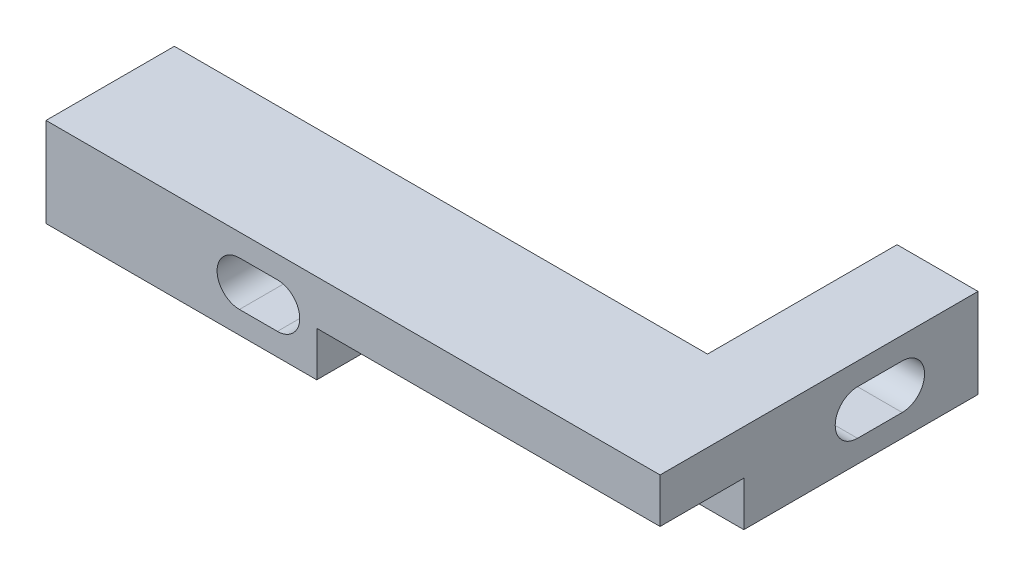
SolidWorks part; units mm, degrees
ref_plane "Front Plane" through (0, 0, 0) normal (0, 0, 1) x (1, 0, 0)
ref_plane "Top Plane" through (0, 0, 0) normal (0, 1, 0) x (1, 0, 0)
ref_plane "Right Plane" through (0, 0, 0) normal (1, 0, 0) x (0, 0, -1)
sketch "Sketch1" plane through (0, 0, 0) normal (0, 1, 0) x (1, 0, 0)
  line L1 (-27.5, 12.5) -> (27.5, 12.5)
  line L2 (-27.5, 12.5) -> (-27.5, -12.5)
  line L3 (-27.5, -12.5) -> (27.5, -12.5)
  line L4 (27.5, 12.5) -> (27.5, -12.5)
  line L5 (-27.5, 12.5) -> (27.5, -12.5) construction
  line L6 (-27.5, -12.5) -> (27.5, 12.5) construction
  point P0 (0, 0)
  dimension "D1" = 55
  dimension "D2" = 25
extrude "Boss-Extrude1" add sketch "Sketch1" along normal blind 4
sketch "Sketch5" plane through (0, 4, 0) normal (0, 1, 0) x (1, 0, 0)
  line L1 (-20.25, 8.5) -> (20.25, 8.5)
  line L2 (-20.25, 8.5) -> (-20.25, -8.5)
  line L3 (-20.25, -8.5) -> (20.25, -8.5)
  line L4 (20.25, 8.5) -> (20.25, -8.5)
  line L5 (-20.25, 8.5) -> (20.25, -8.5) construction
  line L6 (-20.25, -8.5) -> (20.25, 8.5) construction
  point P0 (0, 0)
  dimension "D1" = 17
  dimension "D2" = 40.5
extrude "Cut-Extrude2" cut sketch "Sketch5" against normal through all
sketch "Sketch6" plane through (0, 4, 0) normal (0, 1, 0) x (1, 0, 0)
  line L0 (27.5, -12.5) -> (27.5, 12.5) construction
  line L1 (-27.5, 12.5) -> (27.5, 12.5)
  line L2 (-27.5, 12.5) -> (-27.5, 8.4747)
  line L3 (-27.5, 8.4747) -> (27.5, 8.4747)
  line L4 (27.5, 12.5) -> (27.5, 8.4747)
extrude "Cut-Extrude3" cut sketch "Sketch6" against normal through all
sketch "Sketch13" plane through (0, 4, 0) normal (0, 1, 0) x (1, 0, 0)
  line L2 (20.25, 8.4747) -> (27.5, 8.4747)
  line L3 (20.25, 8.4747) -> (20.25, -12.5)
  line L4 (20.25, -12.5) -> (27.5, -12.5)
  line L5 (27.5, 8.4747) -> (27.5, -12.5)
extrude "Boss-Extrude3" add sketch "Sketch13" against normal blind 8
sketch "Sketch16" plane through (0, 4, 0) normal (0, 1, 0) x (1, 0, 0)
  line L1 (-27.5, -12.5) -> (-20.25, -12.5)
  line L2 (-27.5, -12.5) -> (-27.5, 8.4747)
  line L3 (-27.5, 8.4747) -> (-20.25, 8.4747)
  line L4 (-20.25, -12.5) -> (-20.25, 8.4747)
extrude "Boss-Extrude4" add sketch "Sketch16" against normal blind 8
sketch "Sketch19" plane through (0, 0, 0) normal (0, -1, 0) x (1, 0, 0)
  line L0 (-20.25, 8.5) -> (20.25, 8.5) construction
  line L1 (20.25, 12.5) -> (3.25, 12.5)
  line L2 (20.25, 12.5) -> (20.25, 8.5)
  line L3 (20.25, 8.5) -> (3.25, 8.5)
  line L4 (3.25, 12.5) -> (3.25, 8.5)
  dimension "D1" = 17
extrude "Boss-Extrude5" add sketch "Sketch19" along normal blind 4
sketch "Sketch30" plane through (0, 0, 12.5) normal (0, 0, 1) x (1, 0, 0)
  line L0 (27.5, 4) -> (27.5, -4) construction
  line L1 (-27.5, 4) -> (27.5, 4)
  line L2 (-27.5, 4) -> (-27.5, 0)
  line L3 (-27.5, 0) -> (27.5, 0)
  line L4 (27.5, 4) -> (27.5, 0)
extrude "Boss-Extrude6" add sketch "Sketch30" along normal blind 7.5
sketch "Sketch31" plane through (0, 0, 12.5) normal (0, 0, 1) x (1, 0, 0)
  line L1 (3.25, 0) -> (27.5, 0)
  line L2 (3.25, 0) -> (3.25, -4)
  line L3 (3.25, -4) -> (27.5, -4)
  line L4 (27.5, 0) -> (27.5, -4)
extrude "Boss-Extrude7" add sketch "Sketch31" along normal blind 7.5
sketch "Sketch21" plane through (0, 4, 0) normal (0, 1, 0) x (1, 0, 0)
  line L1 (20.25, -8.5) -> (27.5, -8.5)
  line L2 (20.25, -8.5) -> (20.25, 8.4747)
  line L3 (20.25, 8.4747) -> (27.5, 8.4747)
  line L4 (27.5, -8.5) -> (27.5, 8.4747)
extrude "Cut-Extrude7" cut sketch "Sketch21" against normal through all
sketch "Sketch25" plane through (-27.5, 0, 0) normal (-1, 0, 0) x (0, 0, 1)
  line L0 (2.3145, 0) -> (-1.6855, 0) construction
  line L1 (2.3145, -2) -> (-1.6855, -2)
  line L2 (2.3145, 2) -> (-1.6855, 2)
  arc A0 (2.3145, -2) -> (2.3145, 2) centre (2.3145, 0) ccw
  arc A1 (-1.6855, 2) -> (-1.6855, -2) centre (-1.6855, 0) ccw
  point P3 (0.3145, 0)
  dimension "D1" = 2
  dimension "D2" = 2
extrude "Cut-Extrude9" cut sketch "Sketch25" against normal through all
sketch "Sketch26" plane through (0, 0, 12.5) normal (0, 0, 1) x (1, 0, 0)
  line L1 (-20.25, 0) -> (5.75, 0)
  line L2 (-20.25, 0) -> (-20.25, -3.7687)
  line L3 (-20.25, -3.7687) -> (5.75, -3.7687)
  line L4 (5.75, 0) -> (5.75, -3.7687)
  dimension "D1" = 26
sketch "Sketch29" plane through (0, 0, 12.5) normal (0, 0, 1) x (1, 0, 0)
  line L0 (6.7748, 0) -> (10.1748, 0) construction
  line L1 (6.7748, 2) -> (10.1748, 2)
  line L2 (6.7748, -2) -> (10.1748, -2)
  arc A0 (6.7748, 2) -> (6.7748, -2) centre (6.7748, 0) ccw
  arc A1 (10.1748, -2) -> (10.1748, 2) centre (10.1748, 0) ccw
  point P4 (8.4748, 0)
  dimension "D1" = 1.7
  dimension "D2" = 2
extrude "Cut-Extrude14" cut sketch "Sketch29" against normal through all and the other way through all
mirror "Mirror1"
delete or keep bodies "Body-Delete/Keep 1" type delete bodies bodies 120
